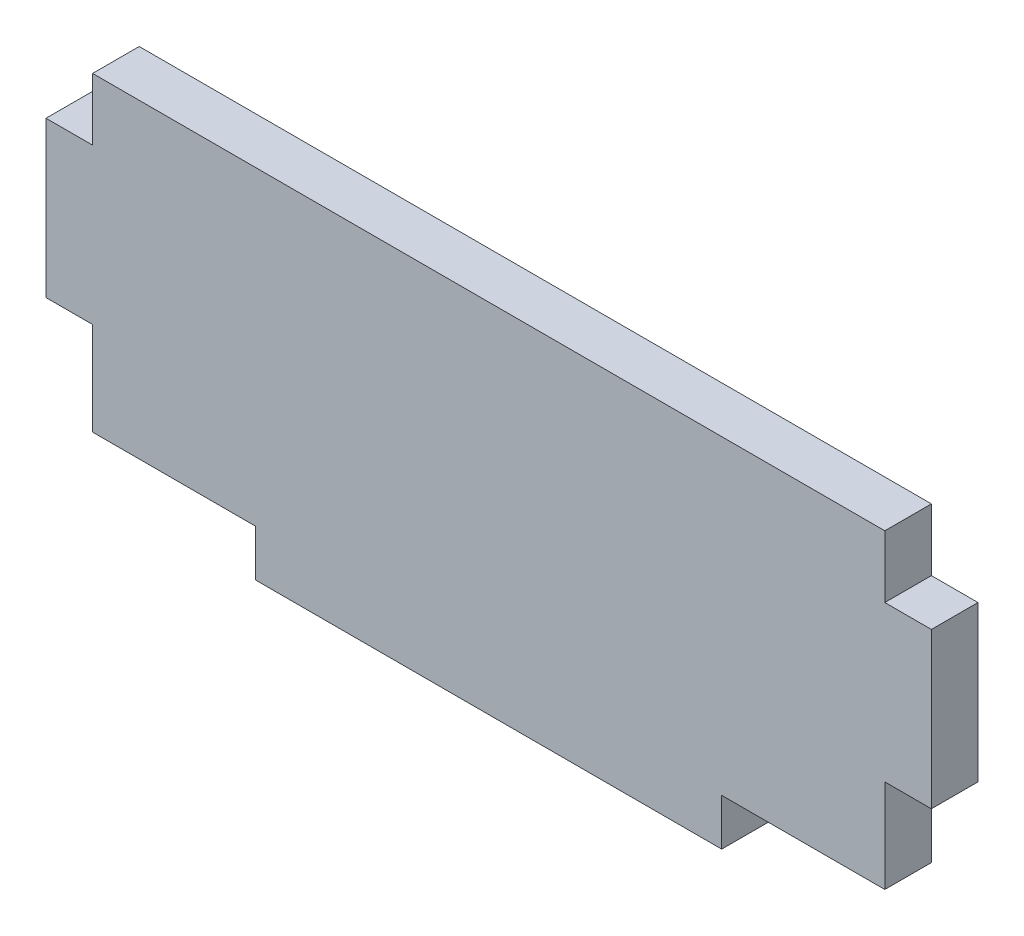
SolidWorks part; units mm, degrees
ref_plane "Front Plane" through (0, 0, 0) normal (0, 0, 1) x (1, 0, 0)
ref_plane "Top Plane" through (0, 0, 0) normal (0, 1, 0) x (1, 0, 0)
ref_plane "Right Plane" through (0, 0, 0) normal (1, 0, 0) x (0, 0, -1)
sketch "Sketch1" plane through (0, 0, 0) normal (0, 0, 1) x (1, 0, 0)
  line L0 (-25.5, -4) -> (-25.5, -10)
  line L1 (-25.5, 10) -> (25.5, 10)
  line L2 (-25.5, 10) -> (-25.5, 6)
  line L3 (-25.5, -10) -> (-15, -10)
  line L4 (25.5, 10) -> (25.5, 6)
  line L5 (-25.5, 10) -> (25.5, -10) construction
  line L6 (-25.5, -10) -> (25.5, 10) construction
  line L7 (-25.5, 6) -> (-28.5, 6)
  line L8 (25.5, -4) -> (25.5, -10)
  line L9 (-25.5, -4) -> (-28.5, -4)
  line L10 (-28.5, 6) -> (-28.5, -4)
  line L12 (-15, -10) -> (-15, -13)
  line L13 (-15, -13) -> (15, -13)
  line L14 (15, -10) -> (15, -13)
  line L15 (25.5, 6) -> (28.5, 6)
  line L16 (15, -10) -> (25.5, -10)
  line L17 (25.5, -4) -> (28.5, -4)
  line L18 (28.5, 6) -> (28.5, -4)
  point P0 (0, 0)
  dimension "D1" = 51
  dimension "D2" = 20
  dimension "D3" = 10.5
  dimension "D4" = 30
  dimension "D5" = 3
  dimension "D6" = 10
  dimension "D7" = 3
  dimension "D8" = 6
  dimension "D9" = 3
  dimension "D10" = 10
  dimension "D11" = 6
extrude "Boss-Extrude1" add sketch "Sketch1" along normal mid plane 3
